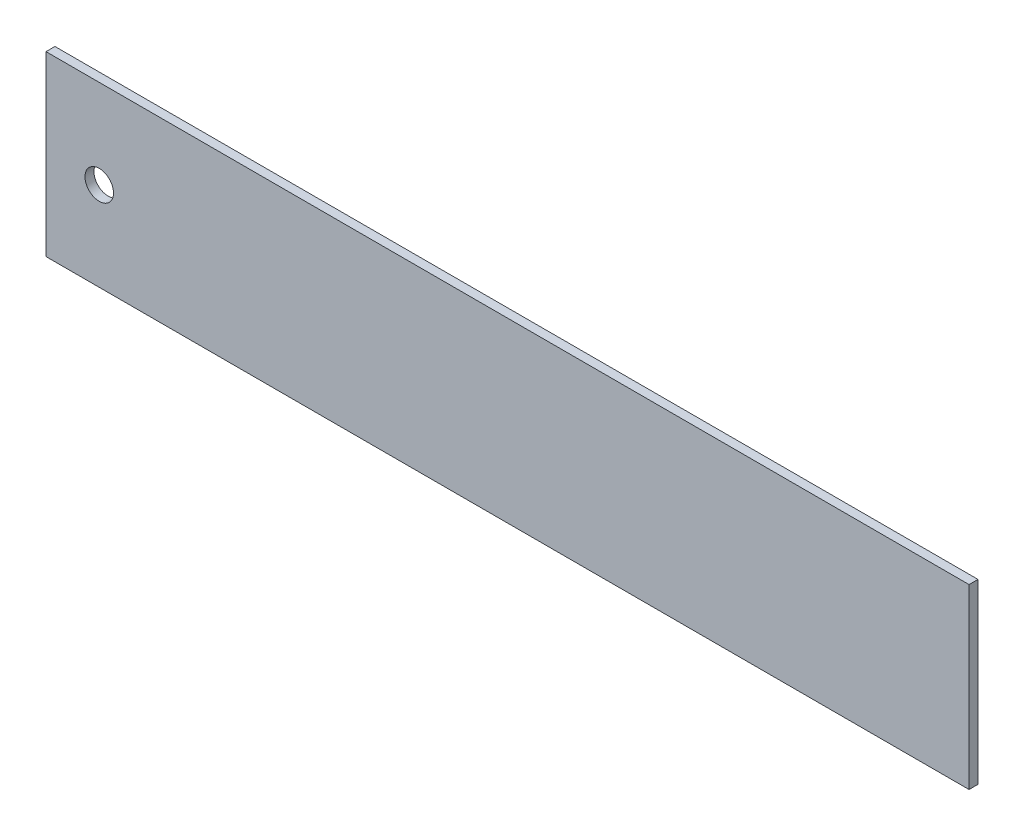
SolidWorks part; units mm, degrees
ref_plane "Front Plane" through (0, 0, 0) normal (0, 0, 1) x (1, 0, 0)
ref_plane "Top Plane" through (0, 0, 0) normal (0, 1, 0) x (1, 0, 0)
ref_plane "Right Plane" through (0, 0, 0) normal (1, 0, 0) x (0, 0, -1)
sketch "Sketch1" plane through (0, 0, 0) normal (0, 0, 1) x (1, 0, 0)
  line L1 (-82.55, 15.875) -> (82.55, 15.875)
  line L2 (-82.55, 15.875) -> (-82.55, -15.875)
  line L3 (-82.55, -15.875) -> (82.55, -15.875)
  line L4 (82.55, 15.875) -> (82.55, -15.875)
  line L5 (-82.55, 15.875) -> (82.55, -15.875) construction
  line L6 (-82.55, -15.875) -> (82.55, 15.875) construction
  point P0 (0, 0)
  dimension "D1" = 165.1
  dimension "D2" = 31.75
extrude "Boss-Extrude1" add sketch "Sketch1" along normal blind 1.6002
sketch "Sketch2" plane through (0, 0, 0) normal (0, 0, -1) x (-1, 0, 0)
  line L0 (82.55, 15.875) -> (82.55, -15.875) construction
  circle A0 centre (73.025, 0) radius 2.5527
  dimension "D1" = 9.525
  dimension "D2" = 5.1054
extrude "Cut-Extrude1" cut sketch "Sketch2" against normal blind 2.54
